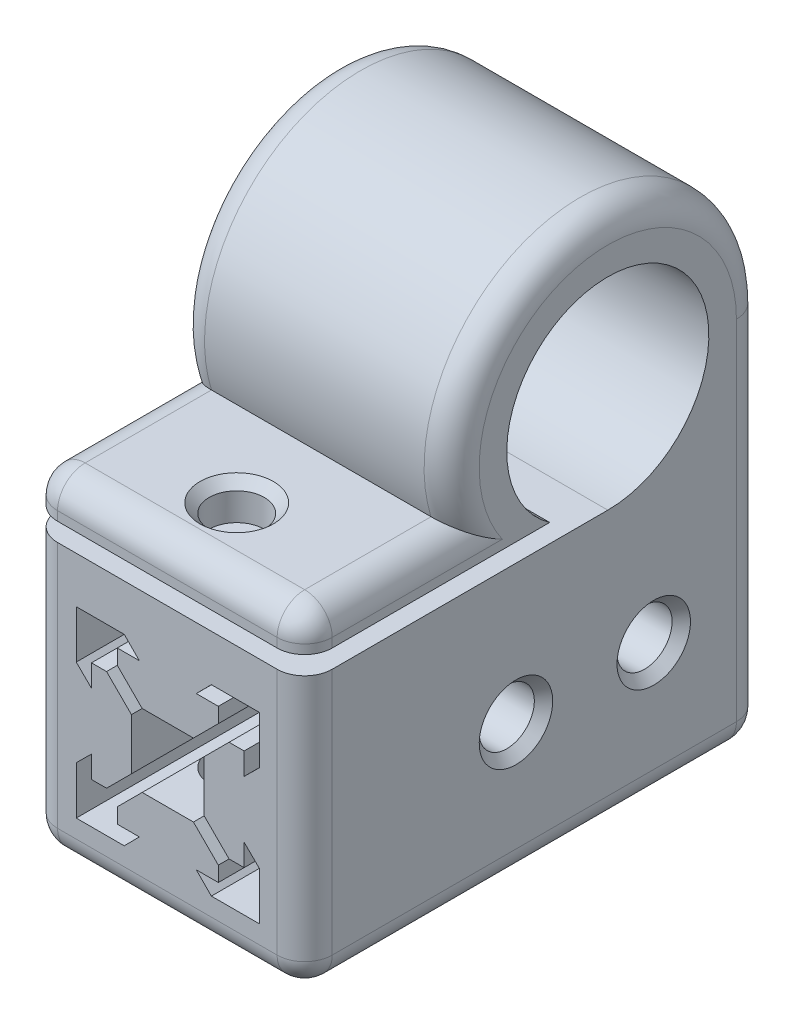
SolidWorks part; units mm, degrees
ref_plane "Front Plane" through (0, 0, 0) normal (0, 0, 1) x (1, 0, 0)
ref_plane "Top Plane" through (0, 0, 0) normal (0, 1, 0) x (1, 0, 0)
ref_plane "Right Plane" through (0, 0, 0) normal (1, 0, 0) x (0, 0, -1)
sketch "Sketch1" plane through (0, 0, 0) normal (0, 0, 1) x (1, 0, 0)
  line L0 (0, -15) -> (0, 15) construction
  line L1 (0, 15) -> (14.8993, 15)
  line L2 (14.8993, 15) -> (14.8993, -14.9496)
  line L3 (14.8993, -14.9496) -> (-15, -14.9496)
  line L4 (-15, -14.9496) -> (-15, 15)
  line L5 (-15, 15) -> (0, 15)
  line L6 (0, -9.9664) -> (0, 9.9664) construction
  line L7 (0, 9.9664) -> (-9.9664, 9.9664) construction
  line L8 (-9.9664, 9.9664) -> (-4.7414, 9.9664)
  line L9 (-4.7414, 9.9664) -> (-3.1, 8.3075)
  line L10 (-3.1, 8.3075) -> (0, 8.3075) construction
  line L11 (-3.1, 8.3075) -> (-5.5, 8.3075)
  line L12 (-5.5, 8.3075) -> (-5.5, 6.6675)
  line L13 (-5.5, 6.6675) -> (-2.79, 3.9575)
  line L14 (-2.79, 3.9575) -> (0, 3.9575) construction
  line L15 (-2.79, 3.9575) -> (2.79, 3.9575)
  line L16 (-9.9664, 9.9664) -> (0, 0) construction
  line L17 (-3.9575, 2.79) -> (-3.9575, -2.79)
  line L18 (-6.6675, 5.5) -> (-3.9575, 2.79)
  line L19 (-8.3075, 5.5) -> (-6.6675, 5.5)
  line L20 (-8.3075, 3.1) -> (-8.3075, 5.5)
  line L21 (-9.9664, 4.7414) -> (-8.3075, 3.1)
  line L22 (-9.9664, 9.9664) -> (-9.9664, 4.7414)
  line L23 (0, 0) -> (-11.0308, 0) construction
  line L24 (5.5, 6.6675) -> (2.79, 3.9575)
  line L25 (5.5, 8.3075) -> (5.5, 6.6675)
  line L26 (3.1, 8.3075) -> (5.5, 8.3075)
  line L27 (4.7414, 9.9664) -> (3.1, 8.3075)
  line L28 (9.9664, 9.9664) -> (4.7414, 9.9664)
  line L29 (9.9664, 9.9664) -> (9.9664, 4.7414)
  line L30 (9.9664, 4.7414) -> (8.3075, 3.1)
  line L31 (8.3075, 3.1) -> (8.3075, 5.5)
  line L32 (8.3075, 5.5) -> (6.6675, 5.5)
  line L33 (6.6675, 5.5) -> (3.9575, 2.79)
  line L34 (3.9575, 2.79) -> (3.9575, -2.79)
  line L35 (-9.9664, -9.9664) -> (0, 0) construction
  line L36 (-2.79, -3.9575) -> (0, -3.9575) construction
  line L37 (-3.1, -8.3075) -> (0, -8.3075) construction
  line L38 (0, -9.9664) -> (-9.9664, -9.9664) construction
  line L39 (6.6675, -5.5) -> (3.9575, -2.79)
  line L40 (8.3075, -5.5) -> (6.6675, -5.5)
  line L41 (8.3075, -3.1) -> (8.3075, -5.5)
  line L42 (9.9664, -4.7414) -> (8.3075, -3.1)
  line L43 (9.9664, -9.9664) -> (9.9664, -4.7414)
  line L44 (9.9664, -9.9664) -> (4.7414, -9.9664)
  line L45 (4.7414, -9.9664) -> (3.1, -8.3075)
  line L46 (3.1, -8.3075) -> (5.5, -8.3075)
  line L47 (5.5, -8.3075) -> (5.5, -6.6675)
  line L48 (5.5, -6.6675) -> (2.79, -3.9575)
  line L49 (-9.9664, -9.9664) -> (-9.9664, -4.7414)
  line L50 (-9.9664, -4.7414) -> (-8.3075, -3.1)
  line L51 (-8.3075, -3.1) -> (-8.3075, -5.5)
  line L52 (-8.3075, -5.5) -> (-6.6675, -5.5)
  line L53 (-6.6675, -5.5) -> (-3.9575, -2.79)
  line L54 (-2.79, -3.9575) -> (2.79, -3.9575)
  line L55 (-5.5, -6.6675) -> (-2.79, -3.9575)
  line L56 (-5.5, -8.3075) -> (-5.5, -6.6675)
  line L57 (-3.1, -8.3075) -> (-5.5, -8.3075)
  line L58 (-4.7414, -9.9664) -> (-3.1, -8.3075)
  line L59 (-9.9664, -9.9664) -> (-4.7414, -9.9664)
  point P43 (3.9575, 0)
  point P58 (-3.9575, 0)
  dimension "D1" = 3.1
  dimension "D2" = 2.79
  dimension "D3" = 2.4
  dimension "D4" = 135
  dimension "D5" = 1.64
  dimension "D6" = 15
  dimension "D7" = 15
  dimension "D8" = 9.9664
  dimension "D9" = 5.225
extrude "Boss-Extrude1" add sketch "Sketch1" along normal blind 50
sketch "Sketch5" plane through (-15, 0, 0) normal (-1, 0, 0) x (0, 0, 1)
  line L0 (0, 15) -> (17, 15) construction
  line L1 (50, 15) -> (0, 15) construction
  line L2 (17, 15) -> (17, 26) construction
  line L3 (0, 26) -> (0, 15)
  line L4 (0, 15) -> (17, 15)
  line L5 (33.2481, 21) -> (50, 21)
  line L6 (50, 21) -> (50, 17)
  line L7 (50, 17) -> (27.8045, 17)
  line L8 (27.8045, 17) -> (23.3246, 17)
  arc A0 (0, 26) -> (33.2481, 21) centre (17, 26) cw
  arc A1 (17, 15) -> (23.3246, 17) centre (17, 26) cw
  dimension "D3" = 17
  dimension "D1" = 2
  dimension "D2" = 4
  dimension "D4" = 11
extrude "Boss-Extrude3" add sketch "Sketch5" against normal through all
sketch "Sketch3" plane through (-15, 0, 0) normal (-1, 0, 0) x (0, 0, 1)
  line L0 (12, 0) -> (50, 0.0252) construction
  line L2 (0, 0) -> (12, 0) construction
  line L3 (50, 15) -> (50, -14.9496) construction
  circle A0 centre (12, 0) radius 3
  circle A1 centre (27, 0) radius 3
  dimension "D1" = 15
extrude "Cut-Extrude1" cut sketch "Sketch3" against normal through all
sketch "Sketch4" plane through (0, 22.0582, 0) normal (0, 1, 0) x (1, 0, 0)
  line L0 (-15, -50) -> (-15, -33.2481) construction
  line L2 (14.8993, -50) -> (-15, -50) construction
  circle A0 centre (0, -42.5) radius 3
  dimension "D1" = 15
  dimension "D2" = 7.5
extrude "Cut-Extrude2" cut sketch "Sketch4" against normal through all
fillet "Fillet1" radius 3 15 edges at (-15, 42.811, 19.5281) (14.8993, 42.811, 19.5281) (-0.0504, -14.9496, 50) (-15, 21, 41.624) (14.8993, 21, 41.624) (-0.0504, 21, 50) (-15, 19, 50) (14.8993, 19, 50) (14.8993, 0.0252, 50) (-15, 0.0252, 50) (14.8993, 5.5252, 0) (-15, 5.5252, 0) (-0.0504, -14.9496, 0) (14.8993, -14.9496, 25) (-15, -14.9496, 25)
chamfer "Chamfer1" distance 1 angle 45 6 edges at (0, -14.9496, 45.5) (14.8993, 0, 30) (14.8993, 0, 15) (-15, 0, 15) (-15, 0, 30) (0, 21, 45.5)
